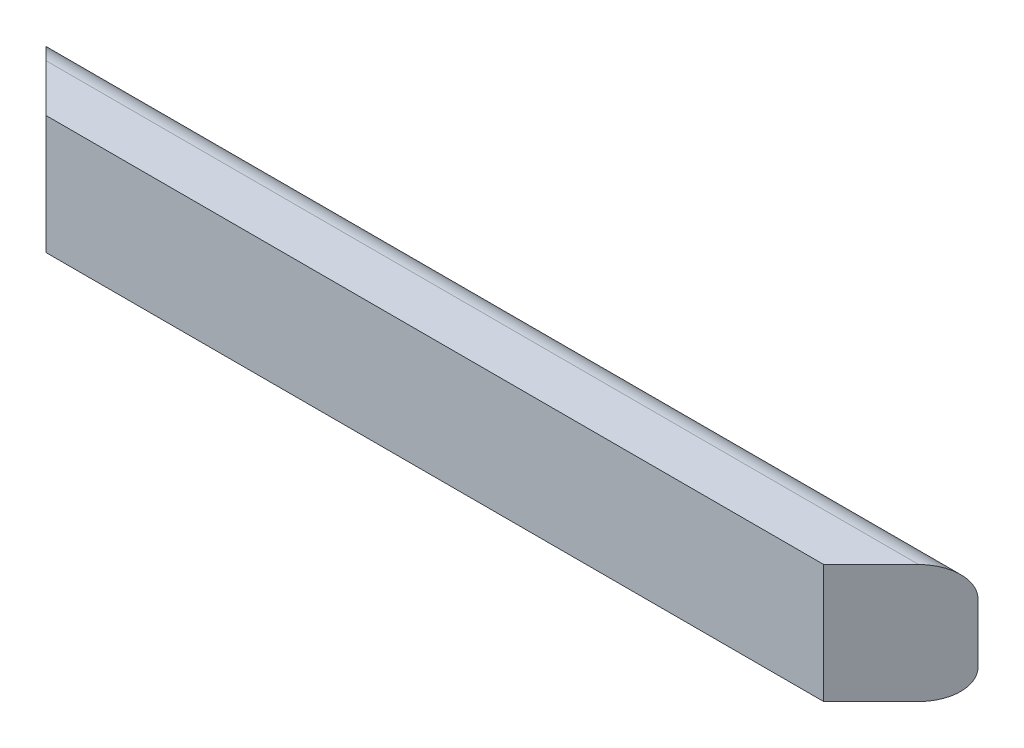
SolidWorks part; units mm, degrees
ref_plane "Front" through (0, 0, 0) normal (0, 0, 1) x (1, 0, 0)
ref_plane "Top" through (0, 0, 0) normal (0, 1, 0) x (1, 0, 0)
ref_plane "Right" through (0, 0, 0) normal (1, 0, 0) x (0, 0, -1)
sketch "Sketch1" plane through (0, 0, 0) normal (1, 0, 0) x (0, 0, -1)
  line L0 (0, 0) -> (0, 127) construction
  line L1 (0, 0) -> (31.75, 0)
  line L2 (31.75, 127) -> (0, 127)
  line L3 (63.5, 95.25) -> (63.5, 31.75)
  line L4 (0, 0) -> (-19.05, 0)
  line L5 (-19.05, 0) -> (-19.05, 127)
  line L6 (-19.05, 127) -> (0, 127)
  arc A0 (31.75, 0) -> (63.5, 31.75) centre (31.75, 31.75) ccw
  arc A1 (63.5, 95.25) -> (31.75, 127) centre (31.75, 95.25) ccw
  dimension "D2" = 63.5
  dimension "D1" = 19.05
extrude "Boss-Extrude1" add sketch "Sketch1" along normal blind 996.95
ref_plane "Mid_Plane" through (498.475, 0, 0) normal (1, 0, 0) x (0, 0, -1)
ref_plane "Plane1" through (466.725, 0, 466.725) normal (0.7071, 0, 0.7071) x (0, 1, 0)
sketch "Sketch2" plane through (466.725, 0, 466.725) normal (0.7071, 0, 0.7071) x (0, 1, 0)
  line L1 (205.1964, -433.0743) -> (-139.2061, -433.0743)
  line L2 (205.1964, -433.0743) -> (205.1964, -926.2875)
  line L3 (205.1964, -926.2875) -> (-139.2061, -926.2875)
  line L4 (-139.2061, -433.0743) -> (-139.2061, -926.2875)
  line L5 (205.1964, -433.0743) -> (-139.2061, -926.2875) construction
  line L6 (205.1964, -926.2875) -> (-139.2061, -433.0743) construction
  point P4 (32.9952, -679.6809)
  point P5 (-139.2061, -926.2875)
extrude "Cut-Extrude1" cut sketch "Sketch2" along normal through all
mirror "Mirror1" about plane through (498.475, 0, 0) normal (1, 0, 0) of "Cut-Extrude1"
